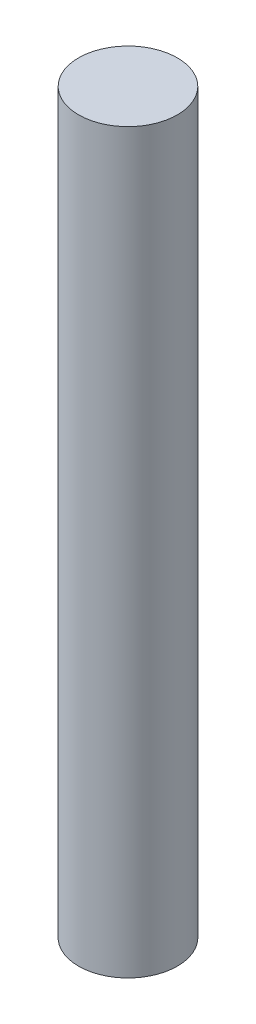
SolidWorks part; units mm, degrees
material "Plain Carbon Steel"
ref_plane "Front Plane" through (0, 0, 0) normal (0, 0, 1) x (1, 0, 0)
ref_plane "Top Plane" through (0, 0, 0) normal (0, 1, 0) x (1, 0, 0)
ref_plane "Right Plane" through (0, 0, 0) normal (1, 0, 0) x (0, 0, -1)
sketch "Sketch1" plane through (0, 0, 0) normal (0, 1, 0) x (1, 0, 0)
  circle A0 centre (0, 0) radius 4.69
  dimension "D1" = 9.38
extrude "Boss-Extrude1" add sketch "Sketch1" along normal blind 70
